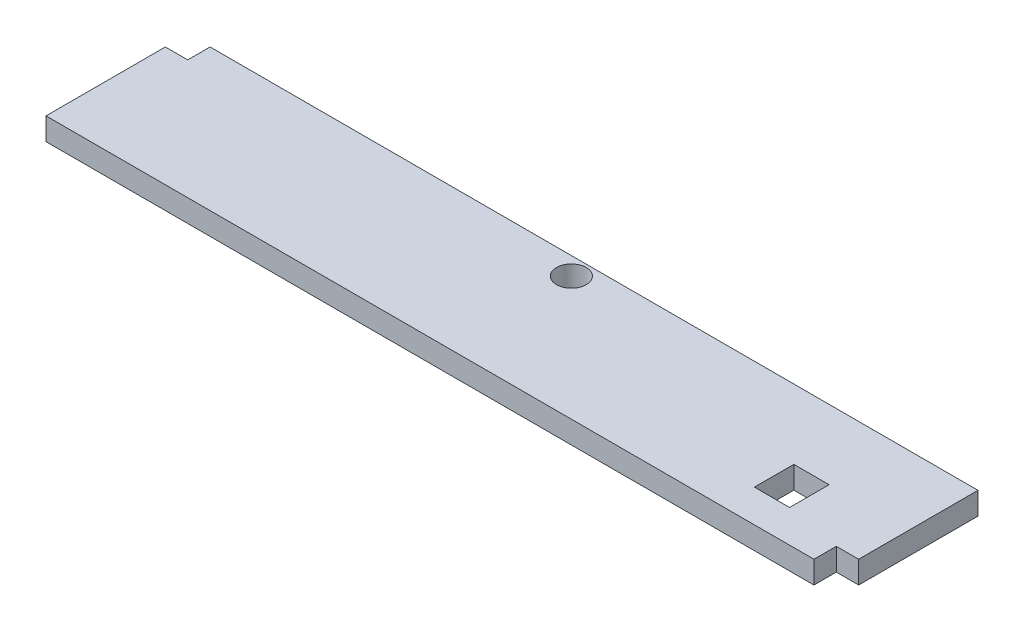
SolidWorks part; units mm, degrees
material "Oak"
ref_plane "Front Plane" through (0, 0, 0) normal (0, 0, 1) x (1, 0, 0)
ref_plane "Top Plane" through (0, 0, 0) normal (0, 1, 0) x (1, 0, 0)
ref_plane "Right Plane" through (0, 0, 0) normal (1, 0, 0) x (0, 0, -1)
sketch "Sketch1" plane through (0, 0, 0) normal (0, 1, 0) x (1, 0, 0)
  line L1 (0, 0) -> (673.1, 0)
  line L2 (0, 0) -> (0, 120.7008)
  line L3 (0, 120.7008) -> (673.1, 120.7008)
  line L4 (673.1, 0) -> (673.1, 120.7008)
  dimension "D1" = 120.7008
  dimension "D2" = 673.1
extrude "Boss-Extrude1" add sketch "Sketch1" along normal blind 19.05
sketch "Sketch3" plane through (0, 0, 0) normal (0, -1, 0) x (1, 0, 0)
  line L1 (605.5366, -61.424) -> (575.523, -61.424)
  line L2 (605.5366, -61.424) -> (605.5366, -27.8088)
  line L3 (605.5366, -27.8088) -> (575.523, -27.8088)
  line L4 (575.523, -61.424) -> (575.523, -27.8088)
extrude "Cut-Extrude5" cut sketch "Sketch3" against normal through all
sketch "Sketch2" plane through (0, 0, 0) normal (0, -1, 0) x (1, 0, 0)
  line L3 (0, -120.7008) -> (0, 0) construction
  line L6 (673.1, -120.7008) -> (0, -120.7008) construction
  circle A0 centre (341.9094, -105.5624) radius 12.7
  dimension "D1" = 25.4
  dimension "D2" = 341.9094
  dimension "D3" = 15.1384
extrude "Cut-Extrude4" cut sketch "Sketch2" against normal through all
sketch "Sketch4" plane through (0, 0, 0) normal (0, -1, 0) x (1, 0, 0)
  line L0 (0, 0) -> (673.1, 0) construction
  line L1 (654.05, 0) -> (673.1, 0)
  line L2 (654.05, 0) -> (654.05, -19.05)
  line L3 (654.05, -19.05) -> (673.1, -19.05)
  line L4 (673.1, 0) -> (673.1, -19.05)
  line L5 (673.1, 0) -> (673.1, -120.7008) construction
  line L6 (673.1, -120.7008) -> (0, -120.7008) construction
  line L7 (0, -120.7008) -> (19.05, -120.7008)
  line L8 (0, -120.7008) -> (0, -101.6508)
  line L9 (0, -101.6508) -> (19.05, -101.6508)
  line L10 (19.05, -120.7008) -> (19.05, -101.6508)
  dimension "D1" = 19.05
  dimension "D2" = 19.05
  dimension "D3" = 19.05
  dimension "D4" = 19.05
extrude "Cut-Extrude6" cut sketch "Sketch4" against normal through all
